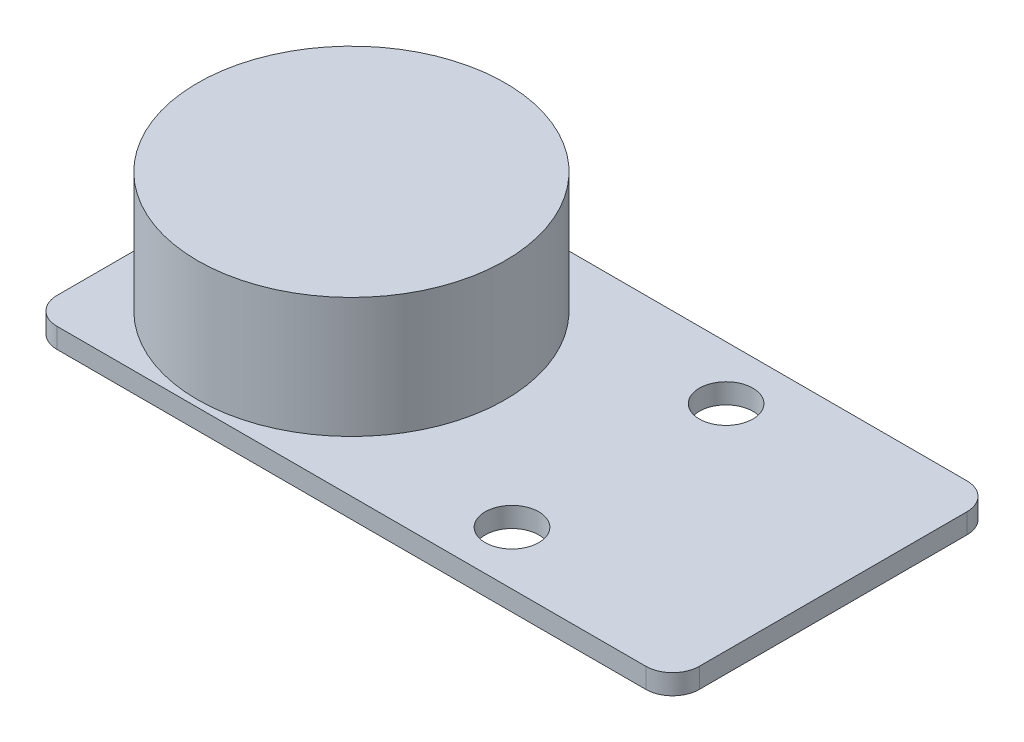
SolidWorks part; units mm, degrees
ref_plane "前视基准面" through (0, 0, 0) normal (0, 0, 1) x (1, 0, 0)
ref_plane "上视基准面" through (0, 0, 0) normal (0, 1, 0) x (1, 0, 0)
ref_plane "右视基准面" through (0, 0, 0) normal (1, 0, 0) x (0, 0, -1)
sketch "草图1" plane through (0, 0, 0) normal (0, 1, 0) x (1, 0, 0)
  line L1 (24, -12) -> (-24, -12)
  line L2 (24, -12) -> (24, 12)
  line L3 (24, 12) -> (-24, 12)
  line L4 (-24, -12) -> (-24, 12)
  line L5 (24, -12) -> (-24, 12) construction
  line L6 (24, 12) -> (-24, -12) construction
  point P0 (0, 0)
  dimension "D1" = 48
  dimension "D2" = 24
extrude "凸台-拉伸1" add sketch "草图1" along normal blind 1.5
fillet "圆角1" radius 2 4 edges at (24, 0.75, 12) (24, 0.75, -12) (-24, 0.75, -12) (-24, 0.75, 12)
sketch "草图2" plane through (0, 1.5, 0) normal (0, 1, 0) x (1, 0, 0)
  line L0 (22, 12) -> (-22, 12) construction
  line L1 (24, -10) -> (24, 10) construction
  line L2 (-24, 0) -> (24, 0) construction
  line L3 (-24, 10) -> (-24, -10) construction
  circle A0 centre (8, 8) radius 2
  circle A1 centre (8, -8) radius 2
  dimension "D2" = 4
  dimension "D1" = 4
  dimension "D3" = 16
extrude "切除-拉伸1" cut sketch "草图2" against normal up to next
sketch "草图3" plane through (0, 1.5, 0) normal (0, 1, 0) x (1, 0, 0)
  line L1 (-24, 10) -> (-24, -10) construction
  circle A0 centre (-12, 0) radius 11.5
  point P4 (0, 0)
  dimension "D1" = 23
  dimension "D2" = 12
extrude "凸台-拉伸2" add sketch "草图3" along normal blind 9
